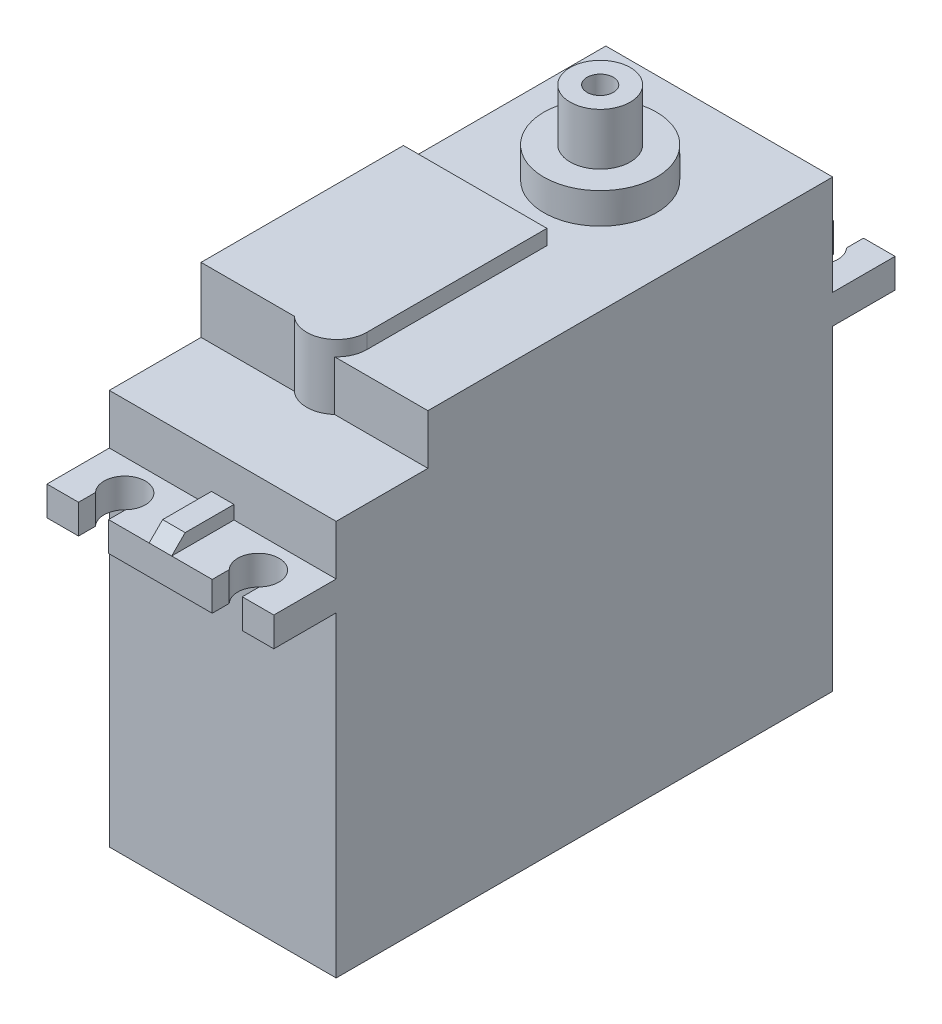
SolidWorks part; units mm, degrees
ref_plane "Front Plane" through (0, 0, 0) normal (0, 0, 1) x (1, 0, 0)
ref_plane "Top Plane" through (0, 0, 0) normal (0, 1, 0) x (1, 0, 0)
ref_plane "Right Plane" through (0, 0, 0) normal (1, 0, 0) x (0, 0, -1)
sketch "Sketch1" plane through (0, 0, 0) normal (1, 0, 0) x (0, 0, -1)
  line L0 (0, 0) -> (66.1, 0)
  line L1 (66.1, 0) -> (66.1, 42.1)
  line L2 (66.1, 42.1) -> (74.4, 42.1)
  line L3 (74.4, 42.1) -> (74.4, 46)
  line L4 (74.4, 46) -> (66.1, 46)
  line L5 (66.1, 46) -> (66.1, 59.3)
  line L6 (66.1, 59.3) -> (12.2136, 59.3)
  line L7 (12.2136, 59.3) -> (12.2136, 52.65)
  line L8 (12.2136, 52.65) -> (0, 52.65)
  line L9 (0, 52.65) -> (0, 46)
  line L10 (0, 46) -> (-8.3, 46)
  line L11 (-8.3, 46) -> (-8.3, 42.1)
  line L12 (-8.3, 42.1) -> (0, 42.1)
  line L13 (0, 42.1) -> (0, 0)
  dimension "D1" = 13.3
extrude "Boss-Extrude1" add sketch "Sketch1" along normal blind 30.2
sketch "Sketch9" plane through (0, 46, 0) normal (0, 1, 0) x (1, 0, 0)
  line L0 (15.1, 74.4) -> (15.1, -8.3) construction
  line L1 (30.2, 74.4) -> (0, 74.4) construction
  line L2 (30.2, -8.3) -> (0, -8.3) construction
  line L4 (22, 74.4) -> (22, 72.1375)
  line L5 (6.2, 74.4) -> (4.2, 74.4)
  line L6 (4.2, 74.4) -> (4.2, 72.1375)
  line L7 (6.2, 74.4) -> (8.2, 74.4)
  line L8 (8.2, 74.4) -> (8.2, 72.1375)
  line L9 (24, 74.4) -> (22, 74.4)
  line L10 (26, 74.4) -> (26, 72.1375)
  line L11 (24, 74.4) -> (26, 74.4)
  line L12 (0, 74.4) -> (0, 33.05) construction
  line L13 (0, 66.1) -> (0, 12.2136) construction
  line L14 (0, 33.05) -> (30.2, 33.05) construction
  line L15 (30.2, 66.1) -> (30.2, 12.2136) construction
  line L17 (24, -8.3) -> (26, -8.3)
  line L18 (26, -8.3) -> (26, -6.0375)
  line L19 (24, -8.3) -> (22, -8.3)
  line L20 (8.2, -8.3) -> (8.2, -6.0375)
  line L21 (6.2, -8.3) -> (8.2, -8.3)
  line L22 (4.2, -8.3) -> (4.2, -6.0375)
  line L23 (6.2, -8.3) -> (4.2, -8.3)
  line L24 (22, -8.3) -> (22, -6.0375)
  arc A0 (4.2, 72.1375) -> (8.2, 72.1375) centre (6.2, 70.25) ccw
  arc A1 (26, 72.1375) -> (22, 72.1375) centre (24, 70.25) cw
  arc A2 (26, -6.0375) -> (22, -6.0375) centre (24, -4.15) ccw
  arc A3 (4.2, -6.0375) -> (8.2, -6.0375) centre (6.2, -4.15) cw
extrude "Cut-Extrude3" cut sketch "Sketch9" against normal blind 6.9
sketch "Sketch10" plane through (0, 59.3, 0) normal (0, 1, 0) x (1, 0, 0)
  line L0 (6.2, 70.25) -> (6.2, 50.25) construction
  line L1 (6.2, 50.25) -> (17.2217, 50.25) construction
  line L2 (15.1, 74.4) -> (15.1, 50.25) construction
  line L3 (22, 74.4) -> (8.2, 74.4) construction
  circle A0 centre (15.1, 50.25) radius 7.5
extrude "Boss-Extrude6" add sketch "Sketch10" along normal blind 4.1
sketch "Sketch11" plane through (0, 63.4, 0) normal (0, 1, 0) x (1, 0, 0)
  circle A0 centre (15.1, 50.25) radius 4
  dimension "D1" = 8
extrude "Boss-Extrude7" add sketch "Sketch11" along normal blind 6.9
ref_plane "Plane3" through (0, 61.3, 0) normal (0, 1, 0) x (1, 0, 0)
sketch "Sketch14" plane through (0, 61.3, 0) normal (0, 1, 0) x (1, 0, 0)
  line L0 (0, 39.1568) -> (15.1, 39.1568)
  line L1 (0, 66.1) -> (0, 12.2136) construction
  line L2 (15.1, 39.1568) -> (19.1, 39.1568)
  line L3 (19.1, 39.1568) -> (19.1, 15.1789)
  line L5 (11.1, 15.1789) -> (0, 15.1789)
  line L6 (0, 15.1789) -> (0, 39.1568)
  arc A0 (11.1, 15.1789) -> (19.1, 15.1789) centre (15.1, 15.1789) ccw
extrude "Boss-Extrude8" add sketch "Sketch14" against normal blind 8.9
sketch "Sketch17" plane through (0, 59.3, 0) normal (0, 1, 0) x (1, 0, 0)
  line L0 (0, 12.2136) -> (15.1537, 12.2136)
  line L1 (15.1537, 12.2136) -> (15.1, 15.1789)
  line L2 (15.1, 15.1789) -> (0, 15.1789)
  line L3 (0, 15.1789) -> (0, 12.2136)
extrude "Boss-Extrude9" add sketch "Sketch17" along normal blind 2
sketch "Sketch18" plane through (0, 46, 0) normal (0, 1, 0) x (1, 0, 0)
  line L0 (15.1, 74.4) -> (16.6, 74.4)
  line L1 (22, 74.4) -> (8.2, 74.4) construction
  line L2 (16.6, 74.4) -> (16.6, 66.1)
  line L3 (30.2, 66.1) -> (0, 66.1) construction
  line L4 (16.6, 66.1) -> (13.6, 66.1)
  line L5 (13.6, 66.1) -> (13.6, 74.4)
  line L6 (13.6, 74.4) -> (15.1, 74.4)
  line L7 (0, 74.4) -> (0, 33.05) construction
  line L8 (0, 33.05) -> (30.2, 33.05) construction
  line L9 (30.2, 66.1) -> (30.2, 12.2136) construction
  line L10 (13.6, -8.3) -> (15.1, -8.3)
  line L11 (13.6, 0) -> (13.6, -8.3)
  line L12 (16.6, 0) -> (13.6, 0)
  line L13 (16.6, -8.3) -> (16.6, 0)
  line L14 (15.1, -8.3) -> (16.6, -8.3)
extrude "Boss-Extrude10" add sketch "Sketch18" along normal blind 1.8
sketch "Sketch22" plane through (16.6, 0, 0) normal (1, 0, 0) x (0, 0, -1)
  line L0 (74.4, 46) -> (72.6, 47.8)
  line L1 (66.1, 47.8) -> (74.4, 47.8) construction
  line L2 (72.6, 47.8) -> (74.4, 47.8)
  line L3 (74.4, 47.8) -> (74.4, 46)
  line L4 (33.05, 0) -> (33.05, 55.6135) construction
  line L5 (0, 0) -> (66.1, 0) construction
  line L6 (-8.3, 47.8) -> (-8.3, 46)
  line L7 (-6.5, 47.8) -> (-8.3, 47.8)
  line L8 (-8.3, 46) -> (-6.5, 47.8)
extrude "Cut-Extrude5" cut sketch "Sketch22" against normal blind 4
sketch "Sketch23" plane through (0, 70.3, 0) normal (0, 1, 0) x (1, 0, 0)
  circle A0 centre (15.1, 50.25) radius 1.75
  dimension "D1" = 3.5
extrude "Cut-Extrude6" cut sketch "Sketch23" against normal blind 7
